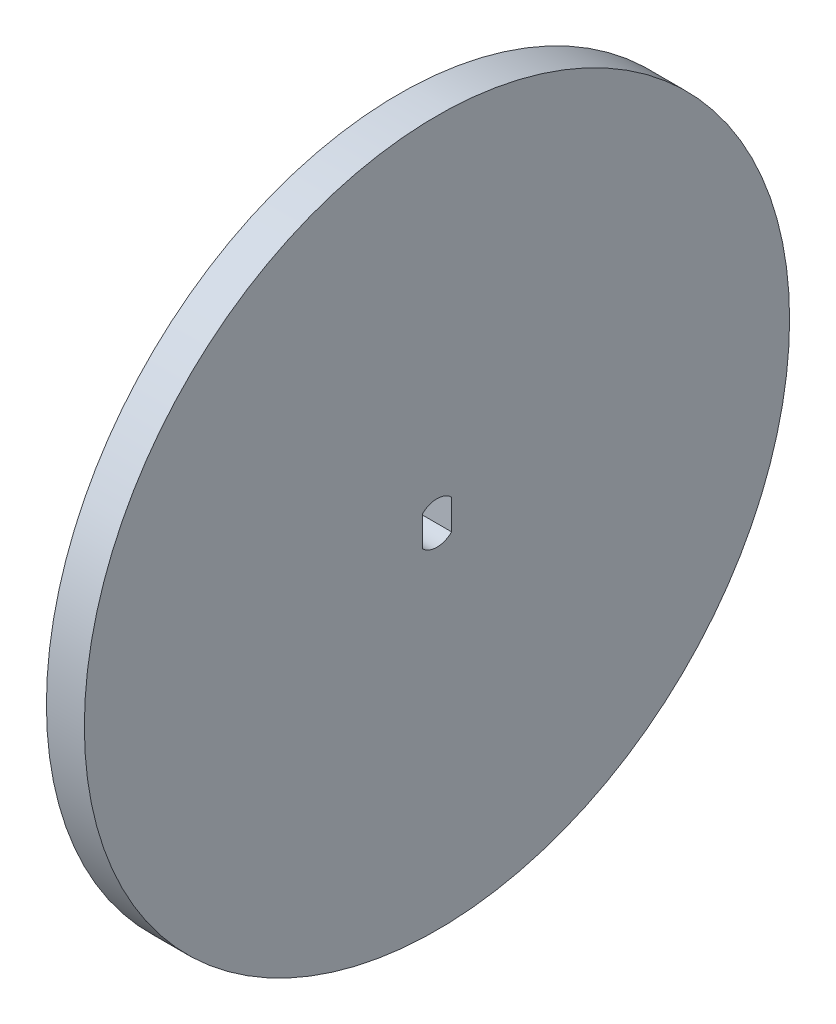
SolidWorks part; units mm, degrees
ref_plane "Alzado" through (0, 0, 0) normal (0, 0, 1) x (1, 0, 0)
ref_plane "Planta" through (0, 0, 0) normal (0, 1, 0) x (1, 0, 0)
ref_plane "Vista lateral" through (0, 0, 0) normal (1, 0, 0) x (0, 0, -1)
sketch "Croquis1" plane through (0, 0, 0) normal (1, 0, 0) x (0, 0, -1)
  line L0 (0, 2.68) -> (0, -2.68) construction
  line L1 (-1.87, 1.9198) -> (-1.87, -1.9198)
  line L2 (1.87, 1.9198) -> (1.87, -1.9198)
  line L3 (1.87, 13.8257) -> (1.87, -10.7169) construction
  line L4 (0, 13.8257) -> (0, -10.7169) construction
  line L5 (-1.87, 13.8257) -> (-1.87, -10.7169) construction
  circle A0 centre (0, 0) radius 45
  arc A1 (1.87, 1.9198) -> (-1.87, 1.9198) centre (0, 0) ccw
  arc A2 (-1.87, -1.9198) -> (1.87, -1.9198) centre (0, 0) ccw
  dimension "D1" = 90
  dimension "D2" = 5.36
  dimension "D3" = 1.87
  dimension "D4" = 1.87
extrude "Saliente-Extruir1" add sketch "Croquis1" along normal blind 4.84
